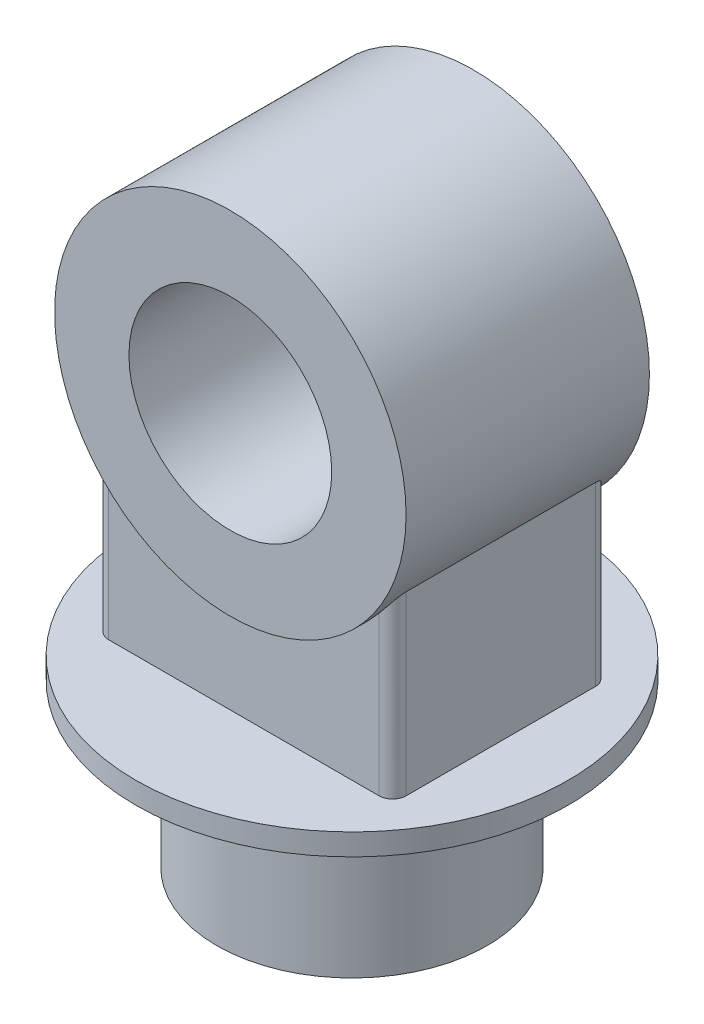
SolidWorks part; units mm, degrees
ref_plane "Front Plane" through (0, 0, 0) normal (0, 0, 1) x (1, 0, 0)
ref_plane "Top Plane" through (0, 0, 0) normal (0, 1, 0) x (1, 0, 0)
ref_plane "Right Plane" through (0, 0, 0) normal (1, 0, 0) x (0, 0, -1)
sketch "Sketch1" plane through (0, 0, 0) normal (0, 1, 0) x (1, 0, 0)
  circle A0 centre (0, 0) radius 100
  dimension "D1" = 200
extrude "Boss-Extrude1" add sketch "Sketch1" along normal blind 120
sketch "Sketch2" plane through (0, 120, 0) normal (0, 1, 0) x (1, 0, 0)
  circle A0 centre (0, 0) radius 160
  dimension "D1" = 320
extrude "Boss-Extrude2" add sketch "Sketch2" along normal blind 16
sketch "Sketch3" plane through (0, 0, 0) normal (0, 0, 1) x (1, 0, 0)
  line L0 (160, 136) -> (-160, 136) construction
  circle A0 centre (0, 336) radius 75
  circle A1 centre (0, 336) radius 130
  dimension "D1" = 150
  dimension "D2" = 260
  dimension "D3" = 200
extrude "Boss-Extrude3" add sketch "Sketch3" along normal mid plane 180 separate body
sketch "Sketch4" plane through (0, 136, 0) normal (0, 1, 0) x (1, 0, 0)
  line L1 (110, -80) -> (-110, -80)
  line L2 (110, -80) -> (110, 80)
  line L3 (110, 80) -> (-110, 80)
  line L4 (-110, -80) -> (-110, 80)
  line L5 (110, -80) -> (-110, 80) construction
  line L6 (110, 80) -> (-110, -80) construction
  point P0 (0, 0)
  dimension "D1" = 160
  dimension "D2" = 220
extrude "Boss-Extrude4" add sketch "Sketch4" along normal up to next
fillet "Fillet1" radius 10 4 edges at (-110, 201.359, 80) (-110, 201.359, -80) (110, 201.359, -80) (110, 201.359, 80)
